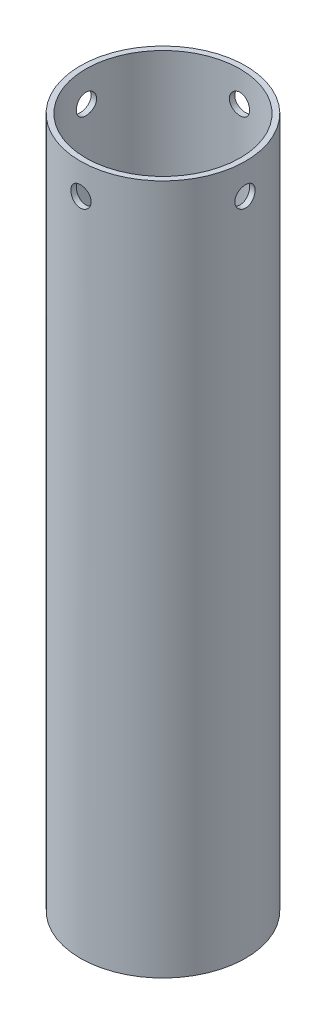
SolidWorks part; units mm, degrees
ref_plane "Ebene vorne" through (0, 0, 0) normal (0, 0, 1) x (1, 0, 0)
ref_plane "Ebene oben" through (0, 0, 0) normal (0, 1, 0) x (1, 0, 0)
ref_plane "Ebene rechts" through (0, 0, 0) normal (1, 0, 0) x (0, 0, -1)
sketch "Skizze1" plane through (0, 0, 0) normal (0, 1, 0) x (1, 0, 0)
  circle A0 centre (0, 0) radius 19
  circle A1 centre (0, 0) radius 20.35
  dimension "D1" = 40.7
  dimension "D2" = 38
extrude "Aufsatz-Linear austragen1" add sketch "Skizze1" along normal blind 170
sketch "Skizze2" plane through (0, 0, 0) normal (0, 0, 1) x (1, 0, 0)
  line L0 (20.35, 170) -> (-20.35, 170) construction
  circle A0 centre (0, 162.5) radius 2.5
  dimension "D2" = 5
  dimension "D1" = 7.5
  dimension "D3" = 0
extrude "Schnitt-Linear austragen1" cut sketch "Skizze2" against normal through all both and the other way through all
sketch "Skizze3" plane through (0, 0, 0) normal (1, 0, 0) x (0, 0, -1)
  line L0 (19, 170) -> (-19, 170) construction
  circle A0 centre (0, 162.5) radius 2.5
  dimension "D3" = 5
  dimension "D1" = 0
  dimension "D2" = 7.5
extrude "Schnitt-Linear austragen2" cut sketch "Skizze3" against normal through all both and the other way through all
